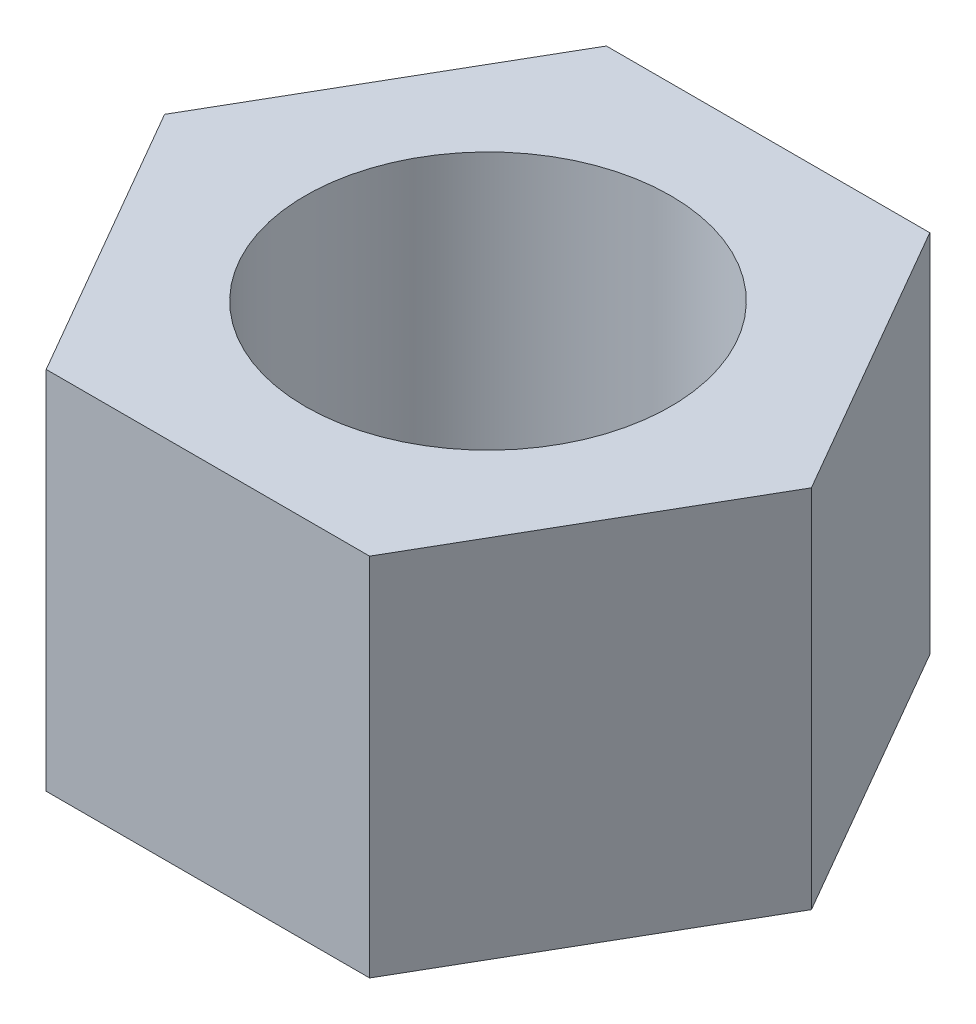
SolidWorks part; units mm, degrees
ref_plane "前视基准面" through (0, 0, 0) normal (0, 0, 1) x (1, 0, 0)
ref_plane "上视基准面" through (0, 0, 0) normal (0, 1, 0) x (1, 0, 0)
ref_plane "右视基准面" through (0, 0, 0) normal (1, 0, 0) x (0, 0, -1)
sketch "草图1" plane through (0, 0, 0) normal (0, 1, 0) x (1, 0, 0)
  line L1 (-1.3279, 2.3) -> (-2.6558, 0)
  line L2 (-2.6558, 0) -> (-1.3279, -2.3)
  line L3 (-1.3279, -2.3) -> (1.3279, -2.3)
  line L4 (1.3279, -2.3) -> (2.6558, 0)
  line L5 (2.6558, 0) -> (1.3279, 2.3)
  line L6 (1.3279, 2.3) -> (-1.3279, 2.3)
  circle A0 centre (0, 0) radius 2.3
  circle A1 centre (0, 0) radius 2.3 construction
  circle A2 centre (0, 0) radius 1.5
  dimension "D1" = 4.6
  dimension "D4" = 3
  dimension "D2" = 4.6
  dimension "D3" = 5.3116
extrude "凸台-拉伸2" add sketch "草图1" along normal blind 3 contours A0 A2 | A0 L6 L1 | A0 L1 L2 | A0 L5 L6 | A0 L4 L5 | A0 L3 L4 | A0 L2 L3
